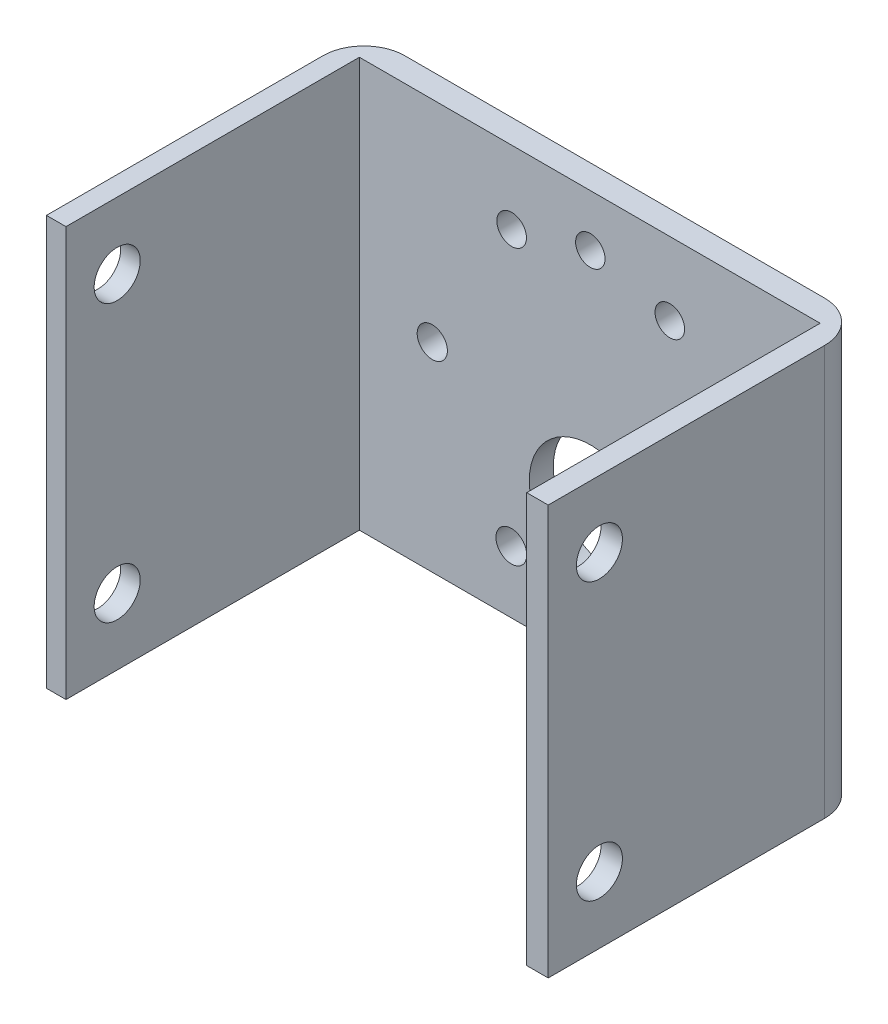
SolidWorks part; units mm, degrees
ref_plane "Front Plane" through (0, 0, 0) normal (0, 0, 1) x (1, 0, 0)
ref_plane "Top Plane" through (0, 0, 0) normal (0, 1, 0) x (1, 0, 0)
ref_plane "Right Plane" through (0, 0, 0) normal (1, 0, 0) x (0, 0, -1)
sketch "Sketch1" plane through (0, 0, 0) normal (0, 1, 0) x (1, 0, 0)
  line L0 (-22.4033, -15.5) -> (-22.4033, 13.1532)
  line L1 (-24.5, 15.5) -> (24.5, 15.5)
  line L2 (-24.5, 15.5) -> (-24.5, -15.5)
  line L3 (-24.5, -15.5) -> (-22.4033, -15.5)
  line L4 (24.5, 15.5) -> (24.5, -15.5)
  line L7 (-22.4033, 13.1532) -> (22.2142, 13.1532)
  line L8 (22.2142, 13.1532) -> (22.2142, -15.5)
  line L10 (22.2142, -15.5) -> (24.5, -15.5)
  point P0 (0, 0)
  dimension "D1" = 31
  dimension "D2" = 49
extrude "Boss-Extrude1" add sketch "Sketch1" along normal blind 40
fillet "Fillet1" radius 4 2 edges at (24.5, 20, -15.5) (-24.5, 20, -15.5)
sketch "Sketch2" plane through (0, 0, -15.5) normal (0, 0, -1) x (-1, 0, 0)
  circle A0 centre (14, 20) radius 1.5
  circle A9 centre (-17, 20) radius 1.5
  circle A10 centre (-1.5, 4.5) radius 1.5
  circle A11 centre (-1.5, 35.5) radius 1.5
  circle A12 centre (-9.25, 6.5766) radius 1.5
  circle A13 centre (-9.25, 33.4234) radius 1.5
  circle A14 centre (6.25, 33.4234) radius 1.5
  circle A15 centre (6.25, 6.5766) radius 1.5
  circle A16 centre (-1.5, 13) radius 6
extrude "Cut-Extrude1" cut sketch "Sketch2" against normal blind 40
sketch "Sketch3" plane through (-24.5, 0, 0) normal (-1, 0, 0) x (0, 0, 1)
  line L0 (15.5, 40) -> (15.5, 0) construction
  line L1 (-11.5, 0) -> (15.5, 0) construction
  line L2 (-11.5, 40) -> (15.5, 40) construction
  circle A0 centre (10.5, 6.5) radius 2.25
  circle A1 centre (10.5, 33.5) radius 2.25
  dimension "D1" = 5
  dimension "D2" = 5
  dimension "D3" = 6.5
  dimension "D4" = 6.5
extrude "Cut-Extrude2" cut sketch "Sketch3" against normal blind 76
sketch "Sketch4" plane through (0, 0, -15.5) normal (0, 0, -1) x (-1, 0, 0)
  circle A0 centre (6.25, 33.4234) radius 1.5
  circle A1 centre (14, 20) radius 1.5
  circle A2 centre (6.25, 6.5766) radius 1.5
  circle A3 centre (-1.5, 4.5) radius 1.5
  circle A4 centre (-9.25, 6.5766) radius 1.5
  circle A5 centre (-17, 20) radius 1.5
  circle A6 centre (-1.5, 35.5) radius 1.5
  circle A7 centre (-9.25, 33.4234) radius 1.5
  circle A8 centre (-1.5, 13) radius 6
extrude "Boss-Extrude2" add sketch "Sketch4" against normal up to surface (2.3468 mm away) up to face at (-15.5, 20, -13.1532)
sketch "Sketch5" plane through (0, 0, -15.5) normal (0, 0, -1) x (-1, 0, 0)
  circle A1 centre (15.5, 20) radius 1.5
  circle A2 centre (0, 4.5) radius 1.5
  circle A3 centre (-15.5, 20) radius 1.5
  circle A4 centre (0, 35.5) radius 1.5
  circle A5 centre (7.75, 33.4234) radius 1.5
  circle A6 centre (-7.75, 33.4234) radius 1.5
  circle A7 centre (-7.75, 6.5766) radius 1.5
  circle A8 centre (7.75, 6.5766) radius 1.5
  circle A9 centre (0, 13) radius 6
extrude "Cut-Extrude3" cut sketch "Sketch5" against normal blind 10
sketch "Sketch7" plane through (0, 0, 0) normal (0, -1, 0) x (1, 0, 0)
  line L0 (-22.4033, -13.1532) -> (-22.5933, -13.1532)
  line L3 (22.2142, 15.5) -> (22.4042, 15.5)
  line L5 (22.2142, -13.1532) -> (22.4042, -13.1532)
  line L6 (22.4042, -13.1532) -> (22.4042, 15.5)
  line L7 (22.2142, -13.1532) -> (22.2142, 15.5)
  line L8 (-22.5933, -13.1532) -> (-22.5933, 15.5)
  line L9 (-24.5, 15.5) -> (-22.4033, 15.5) construction
  line L10 (-22.5933, 15.5) -> (-22.4033, 15.5)
  line L11 (-22.4033, 15.5) -> (-22.4033, -13.1532)
  dimension "D1" = 0.19
  dimension "D2" = 0.19
extrude "Cut-Extrude4" cut sketch "Sketch7" against normal blind 463
sketch "Sketch11" plane through (0, 0, -15.5) normal (0, 0, -1) x (-1, 0, 0)
  circle A0 centre (0, 13) radius 6
extrude "Boss-Extrude3" add sketch "Sketch11" against normal up to surface (2.3468 mm away) up to face at (-1.5, 35.5, -13.1532)
sketch "Sketch12" plane through (0, 0, -15.5) normal (0, 0, -1) x (-1, 0, 0)
  line L1 (-20.5, 0) -> (20.5, 0) construction
  line L2 (-20.5, 40) -> (-20.5, 0) construction
  circle A0 centre (0, 12.5) radius 6
  point P4 (0, 0)
  dimension "D1" = 12.5
  dimension "D2" = 20.5
extrude "Cut-Extrude7" cut sketch "Sketch12" against normal blind 10
sketch "Sketch13" plane through (0, 0, -15.5) normal (0, 0, -1) x (-1, 0, 0)
  circle A0 centre (7.75, 6.5766) radius 1.5
  circle A1 centre (0, 4.5) radius 1.5
  circle A2 centre (-7.75, 6.5766) radius 1.5
  circle A3 centre (-15.5, 20) radius 1.5
  circle A4 centre (-7.75, 33.4234) radius 1.5
  circle A5 centre (0, 35.5) radius 1.5
  circle A6 centre (7.75, 33.4234) radius 1.5
  circle A7 centre (15.5, 20) radius 1.5
extrude "Boss-Extrude4" add sketch "Sketch13" against normal up to surface (2.3468 mm away) up to face at (-6, 12.5, -13.1532)
sketch "Sketch14" plane through (0, 0, -15.5) normal (0, 0, -1) x (-1, 0, 0)
  circle A2 centre (15.4752, 19.4654) radius 1.4756
  circle A3 centre (-15.4752, 19.4654) radius 1.4632
  circle A4 centre (0, 3.9902) radius 1.5
  circle A5 centre (0.0421, 34.9349) radius 1.4349
  circle A6 centre (7.7526, 6.0721) radius 1.5052
  circle A7 centre (-7.7526, 6.0721) radius 1.5
  circle A8 centre (-7.7226, 32.8759) radius 1.4452
  circle A9 centre (7.7226, 32.8759) radius 1.4452
extrude "Cut-Extrude8" cut sketch "Sketch14" against normal blind 10
